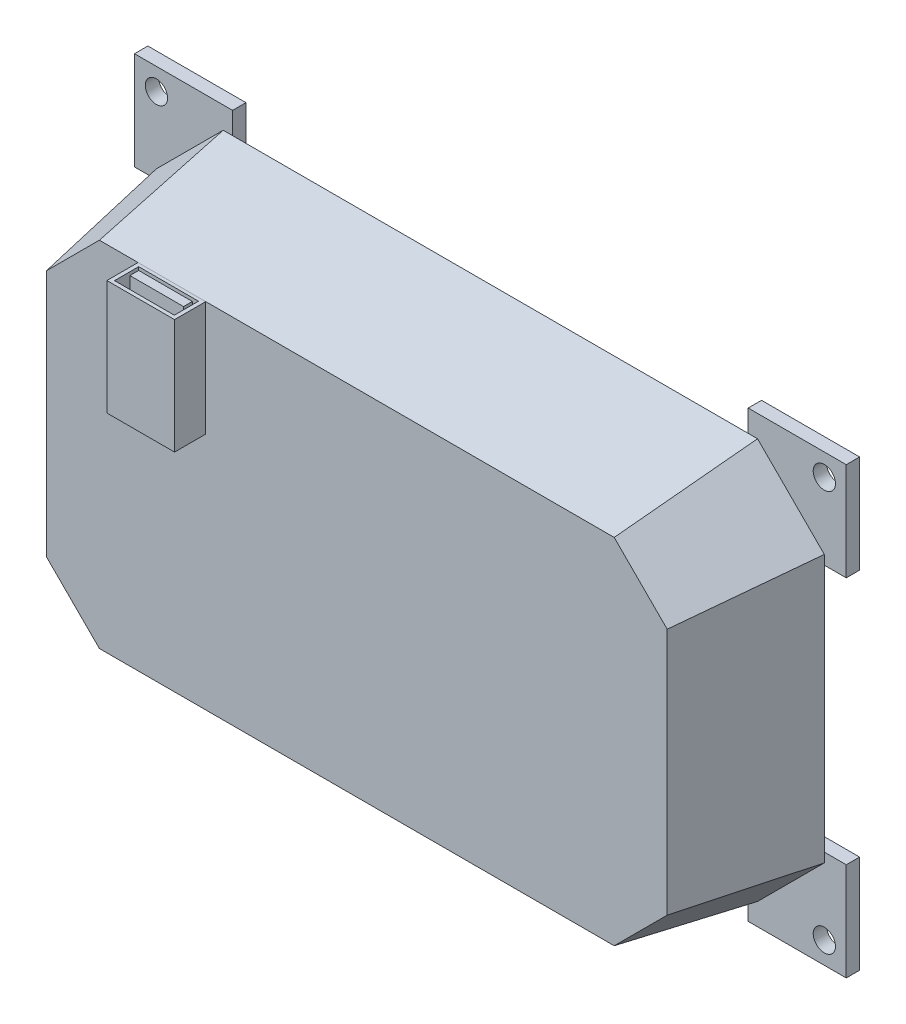
SolidWorks part; units mm, degrees
ref_plane "Front Plane" through (0, 0, 0) normal (0, 0, 1) x (1, 0, 0)
ref_plane "Top Plane" through (0, 0, 0) normal (0, 1, 0) x (1, 0, 0)
ref_plane "Right Plane" through (0, 0, 0) normal (1, 0, 0) x (0, 0, -1)
sketch "Sketch1" plane through (0, 0, 0) normal (0, 0, 1) x (1, 0, 0)
  line L0 (-100, 10.5319) -> (-85, 25.5319)
  line L1 (-85, 25.5319) -> (35, 25.5319)
  line L2 (-100, 10.5319) -> (-100, -49.4681)
  line L3 (-85, -64.4681) -> (35, -64.4681)
  line L4 (50, 10.5319) -> (50, -49.4681)
  line L5 (35, 25.5319) -> (50, 10.5319)
  line L6 (-100, -49.4681) -> (-85, -64.4681)
  line L7 (35, -64.4681) -> (50, -49.4681)
  point P0 (0, 0)
  point P1 (50, -64.4681)
  point P2 (-100, 25.5319)
  point P3 (-100, -64.4681)
  point P4 (50, 25.5319)
  dimension "D1" = 150
  dimension "D2" = 90
extrude "Boss-Extrude1" add sketch "Sketch1" along normal blind 30 draft 10
shell "Shell1" thickness 5
sketch "Sketch4" plane through (0, 0, -10) normal (0, 0, -1) x (-1, 0, 0)
  circle A0 centre (-24.7585, -65.1412) radius 1.5
  dimension "D1" = 3
ref_plane "Plane1" through (-26.0656, 0, 0) normal (1, 0, 0) x (0, 0, -1)
ref_plane "Plane2" through (0, -19.4681, 0) normal (0, 1, 0) x (1, 0, 0)
sketch "Sketch6" plane through (0, 0, 30) normal (0, 0, 1) x (1, 0, 0)
  line L0 (32.8089, 20.2421) -> (-82.8089, 20.2421) construction
  line L1 (-74.1243, -5.5302) -> (-58.9267, -5.5302)
  line L2 (-74.1243, -5.5302) -> (-74.1243, 20.2421)
  line L3 (-74.1243, 20.2421) -> (-58.9267, 20.2421)
  line L4 (-58.9267, -5.5302) -> (-58.9267, 20.2421)
  line L5 (-74.1243, -5.5302) -> (-58.9267, 20.2421) construction
  line L6 (-74.1243, 20.2421) -> (-58.9267, -5.5302) construction
  point P0 (-66.5255, 7.356)
extrude "Boss-Extrude4" add sketch "Sketch6" along normal blind 7
sketch "Sketch7" plane through (0, 20.2421, 0) normal (0, 1, 0) x (1, 0, 0)
  line L1 (-73.2445, -30.7397) -> (-59.8107, -30.7397)
  line L2 (-73.2445, -30.7397) -> (-73.2445, -36.1685)
  line L3 (-73.2445, -36.1685) -> (-59.8107, -36.1685)
  line L4 (-59.8107, -30.7397) -> (-59.8107, -36.1685)
  line L5 (-72.5084, -31.4758) -> (-60.4548, -31.4758)
  line L6 (-72.5084, -31.4758) -> (-72.5084, -33.4541)
  line L7 (-72.5084, -33.4541) -> (-60.4548, -33.4541)
  line L8 (-60.4548, -31.4758) -> (-60.4548, -33.4541)
extrude "Cut-Extrude2" cut sketch "Sketch7" against normal blind 17
sketch "Sketch8" plane through (0, 0, 0) normal (0, 0, -1) x (-1, 0, 0)
  line L0 (-50, 10.5319) -> (-52.108, 21.8062)
  line L1 (-46.2742, 27.64) -> (-35, 25.5319)
  line L2 (-50, 10.5319) -> (-50, 3.2841)
  line L3 (-50, 3.2841) -> (-27.7522, 25.5319)
  line L5 (-27.7522, 25.5319) -> (-35, 25.5319)
  line L7 (-35, 25.5319) -> (85, 25.5319) construction
  arc A0 (-52.108, 21.8062) -> (-46.2742, 27.64) centre (-47.1932, 22.7251) cw
  circle A1 centre (-46.2742, 21.8062) radius 2.5
  dimension "D1" = 5
  dimension "D2" = 5
ref_plane "Plane3" through (0, -19.4681, 0) normal (0, -1, 0) x (-1, 0, 0)
ref_plane "Plane4" through (-25, 0, 0) normal (1, 0, 0) x (0, 0, -1)
ref_plane "Plane5" through (0, -19.4681, 0) normal (0, 1, 0) x (1, 0, 0)
ref_plane "Plane6" through (-25, 0, 0) normal (1, 0, 0) x (0, 0, -1)
sketch "Sketch11" plane through (0, 0, 0) normal (0, 0, -1) x (-1, 0, 0)
  line L0 (94.9229, -47.3651) -> (82.897, -59.3909) construction
  line L1 (94.9229, -47.3651) -> (82.897, -59.3909)
  line L2 (82.897, -59.3909) -> (82.897, -69.3909)
  line L3 (82.897, -69.3909) -> (104.9229, -69.3909)
  line L4 (104.9229, -69.3909) -> (104.9229, -47.3651)
  line L5 (104.9229, -47.3651) -> (94.9229, -47.3651)
  dimension "D1" = 10
extrude "Boss-Extrude6" add sketch "Sketch11" along normal blind 3
mirror "Mirror8" about plane through (-25, 0, 0) normal (1, 0, 0) of "Boss-Extrude6"
mirror "Mirror9" about plane through (0, -19.4681, 0) normal (0, 1, 0) of "Boss-Extrude6", "Mirror8"
sketch "Sketch12" plane through (0, 0, 0) normal (0, 0, 1) x (1, 0, 0)
  circle A0 centre (-100, -64.4681) radius 2.5 construction
  circle A1 centre (-100, -64.4681) radius 2.5
extrude "Cut-Extrude4" cut sketch "Sketch12" against normal through all both and the other way through all
mirror "Mirror10" about plane through (-25, 0, 0) normal (1, 0, 0) of "Cut-Extrude4"
mirror "Mirror11" about plane through (0, -19.4681, 0) normal (0, 1, 0) of "Cut-Extrude4", "Mirror10"
